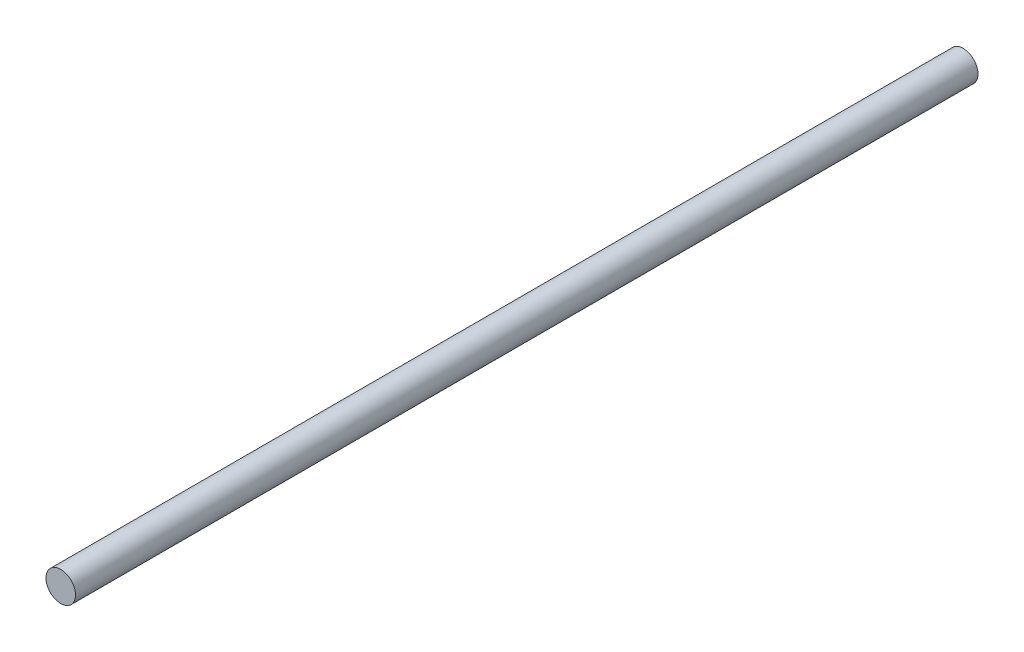
SolidWorks part; units mm, degrees
ref_plane "Front Plane" through (0, 0, 0) normal (0, 0, 1) x (1, 0, 0)
ref_plane "Top Plane" through (0, 0, 0) normal (0, 1, 0) x (1, 0, 0)
ref_plane "Right Plane" through (0, 0, 0) normal (1, 0, 0) x (0, 0, -1)
sketch "Sketch1" plane through (0, 0, 0) normal (0, 0, 1) x (1, 0, 0)
  circle A0 centre (0, 0) radius 0.5
extrude "Boss-Extrude1" add sketch "Sketch1" along normal blind 30.5
